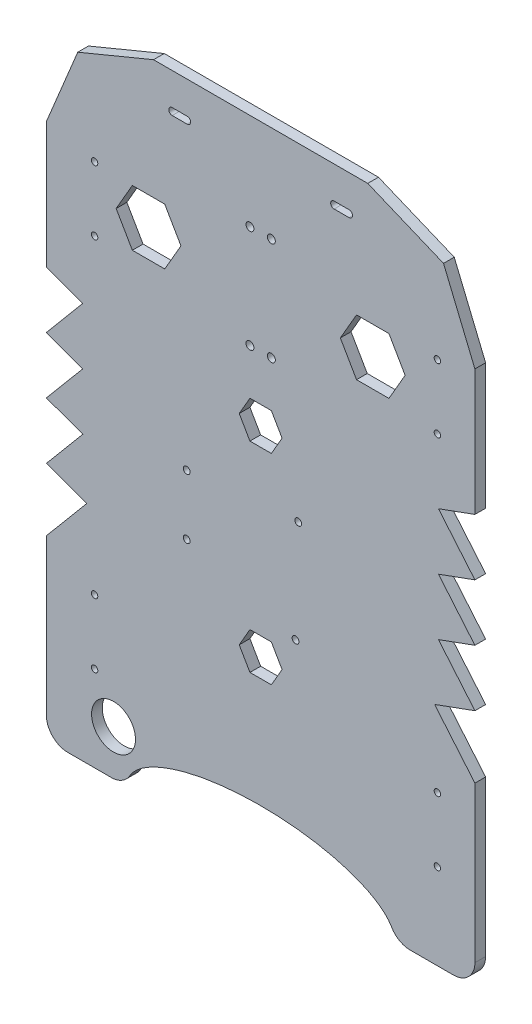
SolidWorks part; units mm, degrees
ref_plane "前视基准面" through (0, 0, 0) normal (0, 0, 1) x (1, 0, 0)
ref_plane "上视基准面" through (0, 0, 0) normal (0, 1, 0) x (1, 0, 0)
ref_plane "右视基准面" through (0, 0, 0) normal (1, 0, 0) x (0, 0, -1)
sketch "草图1" plane through (0, 0, 0) normal (0, 0, 1) x (1, 0, 0)
  line L0 (-34.522, -8.1881) -> (17.5507, -3.1071)
  line L1 (100, -150) -> (-100, -150)
  line L2 (100, -150) -> (100, 100)
  line L3 (50, 150) -> (-50, 150)
  line L4 (-100, -150) -> (-100, 100)
  line L5 (100, -150) -> (-100, 150) construction
  line L6 (100, 150) -> (-100, -150) construction
  line L7 (17.5507, -3.1071) -> (16.2847, -51.3573)
  line L8 (16.2847, -51.3573) -> (-34.522, -36.1281)
  line L9 (-34.522, -36.1281) -> (-34.522, -8.1881)
  arc A0 (100, 100) -> (50, 150) centre (50, 100) ccw
  arc A1 (-50, 150) -> (-100, 100) centre (-50, 100) ccw
  circle A2 centre (-34.522, -8.1881) radius 1.6
  circle A3 centre (17.5507, -3.1071) radius 1.6
  circle A4 centre (16.2847, -51.3573) radius 1.6
  circle A5 centre (-34.522, -36.1281) radius 1.6
  point P0 (0, 0)
  dimension "D3" = 50
  dimension "D9" = 3.2
  dimension "D10" = 3.2
  dimension "D11" = 3.2
  dimension "D12" = 3.2
  dimension "D1" = 200
  dimension "D2" = 300
  dimension "D4" = 27.94
  dimension "D5" = 66.67
  dimension "D6" = 52.32
  dimension "D7" = 61.66
  dimension "D8" = 53.04
extrude "凸台-拉伸1" add sketch "草图1" against normal blind 5 contours L3 A1 L4 L1 L2 A0 A5 L9 A2 L0 A3 L7 A4 L8 | A5 L8 A4 L7 A3 L0 A2 L9
sketch "草图2" plane through (0, 0, 0) normal (0, 0, 1) x (1, 0, 0)
  line L0 (50, 150) -> (-50, 150) construction
  line L1 (-77.5, 95) -> (82.5, 95)
  line L2 (-77.5, 95) -> (-77.5, 65)
  line L3 (-77.5, 65) -> (82.5, 65)
  line L4 (82.5, 95) -> (82.5, 65)
  line L5 (-77.5, -80) -> (82.5, -80)
  line L6 (-77.5, -80) -> (-77.5, -110)
  line L7 (-77.5, -110) -> (82.5, -110)
  line L8 (82.5, -80) -> (82.5, -110)
  line L9 (100, -150) -> (100, 100) construction
  line L10 (100, -150) -> (-100, -150) construction
  circle A0 centre (-77.5, 95) radius 1.5
  circle A1 centre (-77.5, 65) radius 1.5
  circle A2 centre (82.5, 95) radius 1.5
  circle A3 centre (82.5, 65) radius 1.5
  circle A4 centre (82.5, -80) radius 1.5
  circle A5 centre (82.5, -110) radius 1.5
  circle A6 centre (-77.5, -110) radius 1.5
  circle A7 centre (-77.5, -80) radius 1.5
  dimension "D9" = 3
  dimension "D1" = 55
  dimension "D2" = 17.5
  dimension "D3" = 160
  dimension "D4" = 30
  dimension "D5" = 40
  dimension "D6" = 30
  dimension "D7" = 17.5
  dimension "D8" = 160
extrude "切除-拉伸1" cut sketch "草图2" against normal blind 10 contours L1 A0 L2 | L2 A0 L1 | L2 A1 L3 | L3 A1 L2 | L4 A2 L1 | L1 A2 L4 | L3 A3 L4 | L4 A3 L3 | L5 A4 L8 | L7 A5 L8 | L8 A4 L5 | L8 A5 L7 | L7 A6 L6 | L6 A6 L7 | L6 A7 L5 | L5 A7 L6
sketch "草图3" plane through (0, 0, 0) normal (0, 0, 1) x (1, 0, 0)
  line L0 (0, 150) -> (0, -150) construction
  line L1 (50, 150) -> (-50, 150) construction
  line L2 (100, -150) -> (-100, -150) construction
  circle A0 centre (-5, 105) radius 1.85
  circle A1 centre (5, 105) radius 1.85
  circle A2 centre (-5, 57) radius 1.85
  circle A3 centre (5, 57) radius 1.85
  dimension "D2" = 3.7
  dimension "D4" = 3.7
  dimension "D1" = 10
  dimension "D3" = 45
  dimension "D5" = 48
  dimension "D6" = 10
extrude "切除-拉伸2" cut sketch "草图3" against normal blind 10
sketch "草图4" plane through (0, 0, 0) normal (0, 0, 1) x (1, 0, 0)
  circle A0 centre (-68.6677, -128.9563) radius 10.25
  dimension "D1" = 20.5
extrude "切除-拉伸3" cut sketch "草图4" against normal blind 10
sketch "草图5" plane through (0, 0, 0) normal (0, 0, 1) x (1, 0, 0)
  line L0 (100, -150) -> (-100, -150) construction
  ellipse E0 centre (0, -150) end of major axis (62.5366, -150) minor radius 23.4961
extrude "切除-拉伸4" cut sketch "草图5" against normal blind 10
fillet "圆角1" radius 10 4 edges at (100, -150, -2.5) (62.5366, -150, -2.5) (-62.5366, -150, -2.5) (-100, -150, -2.5)
sketch "草图6" plane through (0, 0, 0) normal (0, 0, 1) x (1, 0, 0)
  line L0 (44.7566, 68.037) -> (37.195, 81.1341)
  line L3 (50, 150) -> (-50, 150) construction
  line L4 (0, 150) -> (0, -126.5039) construction
  line L11 (-37.195, 81.1341) -> (-44.7566, 94.2313)
  line L12 (-44.7566, 94.2313) -> (-59.8799, 94.2313)
  line L13 (-59.8799, 94.2313) -> (-67.4415, 81.1341)
  line L14 (-67.4415, 81.1341) -> (-59.8799, 68.037)
  line L15 (-59.8799, 68.037) -> (-44.7566, 68.037)
  line L16 (-44.7566, 68.037) -> (-37.195, 81.1341)
  line L17 (59.8799, 68.037) -> (44.7566, 68.037)
  line L18 (67.4415, 81.1341) -> (59.8799, 68.037)
  line L19 (59.8799, 94.2313) -> (67.4415, 81.1341)
  line L20 (44.7566, 94.2313) -> (59.8799, 94.2313)
  line L21 (37.195, 81.1341) -> (44.7566, 94.2313)
  circle A2 centre (-52.3182, 81.1341) radius 13.0971 construction
  ellipse E0 centre (0, -150) end of major axis (62.5366, -150) minor radius 23.4961 (61.1091, -145.0084) -> (-61.1091, -145.0084) ccw construction
extrude "切除-拉伸5" cut sketch "草图6" against normal blind 10
sketch "草图9" plane through (0, 0, 0) normal (0, 0, 1) x (1, 0, 0)
  line L0 (-100, 41.1875) -> (-83, 35)
  line L1 (-100, -140) -> (-100, 100) construction
  line L2 (-83, 35) -> (-100, 14.7402)
  line L3 (-100, 14.7402) -> (-83, 8.5527)
  line L4 (-83, 8.5527) -> (-100, -11.7071)
  line L5 (-100, -11.7071) -> (-83, -17.8946)
  line L6 (-83, -17.8946) -> (-100, -38.1544)
  line L7 (-100, -38.1544) -> (-81.1919, -45)
  line L8 (-81.1919, -45) -> (-100, -67.4146)
  line L9 (0, 150) -> (0, -126.5039) construction
  line L10 (50, 150) -> (-50, 150) construction
  line L11 (81.1919, -45) -> (100, -67.4146)
  line L12 (100, -38.1544) -> (81.1919, -45)
  line L13 (83, -17.8946) -> (100, -38.1544)
  line L14 (100, -11.7071) -> (83, -17.8946)
  line L15 (83, 8.5527) -> (100, -11.7071)
  line L16 (100, 14.7402) -> (83, 8.5527)
  line L17 (83, 35) -> (100, 14.7402)
  line L18 (100, 41.1875) -> (83, 35)
  line L19 (-100, 41.1875) -> (-100, -67.4146)
  line L20 (100, 41.1875) -> (100, -67.4146)
  line L21 (-69.7645, -150) -> (-90, -150) construction
  ellipse E0 centre (0, -150) end of major axis (62.5366, -150) minor radius 23.4961 (61.1091, -145.0084) -> (-61.1091, -145.0084) ccw construction
  point P32 (0, 0)
  point P33 (0, 0)
  point P34 (-83.7909, -150)
  point P37 (0, 0)
  line M38 (100, -140) -> (100, 100)
  line M42 (-100, 100) -> (-100, -140)
  dimension "D1" = 70
  dimension "D2" = 70
  dimension "D3" = 40
  dimension "D4" = 17
  dimension "D5" = 17
  dimension "D6" = 17
  dimension "D7" = 105
  dimension "D8" = 115
extrude "切除-拉伸6" cut sketch "草图9" against normal blind 10 contours L2 L0 M42 | L4 L3 M42 | L6 L5 M42 | L8 L7 M42 | L12 L11 M38 | L14 L13 M38 | L16 L15 M38 | L18 L17 M38
sketch "草图10" plane through (0, 0, 0) normal (0, 0, 1) x (1, 0, 0)
  line L0 (0, 150) -> (0, -126.5039)
  line L1 (50, 150) -> (-50, 150) construction
  line L3 (10, 27) -> (5, 35.6603)
  line L4 (5, 35.6603) -> (-5, 35.6603)
  line L5 (-5, 35.6603) -> (-10, 27)
  line L6 (-10, 27) -> (-5, 18.3397)
  line L7 (-5, 18.3397) -> (5, 18.3397)
  line L8 (5, 18.3397) -> (10, 27)
  line L9 (10, -66.5039) -> (5, -57.8436)
  line L10 (5, -57.8436) -> (-5, -57.8436)
  line L11 (-5, -57.8436) -> (-10, -66.5039)
  line L12 (-10, -66.5039) -> (-5, -75.1641)
  line L13 (-5, -75.1641) -> (5, -75.1641)
  line L14 (5, -75.1641) -> (10, -66.5039)
  circle A0 centre (0, 27) radius 10
  circle A1 centre (0, -66.5039) radius 10
  circle A2 centre (0, 27) radius 8.6603 construction
  circle A3 centre (0, -66.5039) radius 8.6603 construction
  ellipse E0 centre (0, -150) end of major axis (62.5366, -150) minor radius 23.4961 (61.1091, -145.0084) -> (-61.1091, -145.0084) ccw construction
  dimension "D1" = 20
  dimension "D2" = 20
  dimension "D3" = 123
  dimension "D4" = 60
extrude "切除-拉伸7" cut sketch "草图10" against normal blind 10 contours L0 A0 | L0 A0 | L0 A1 | L0 A1
sketch "草图12" plane through (0, 0, -5) normal (0, 0, -1) x (-1, 0, 0)
  line L0 (-100, 100) -> (-85.3553, 135.3553)
  line L1 (50, 150) -> (85.3553, 135.3553)
  line L2 (85.3553, 135.3553) -> (100, 100)
  line L3 (-85.3553, 135.3553) -> (-50, 150)
  arc A0 (100, 100) -> (50, 150) centre (50, 100) ccw construction
  arc A1 (-50, 150) -> (-100, 100) centre (-50, 100) ccw construction
  circle A2 centre (-50, 100) radius 50
  circle A3 centre (50, 100) radius 50
extrude "切除-拉伸8" cut sketch "草图12" against normal blind 10 contours L0 A2 | L3 A2 | L1 A3 | L2 A3
sketch "草图13" plane through (0, 0, -5) normal (0, 0, -1) x (-1, 0, 0)
  line L0 (0, 150) -> (0, -126.5039)
  line L1 (-50, 150) -> (50, 150) construction
  line L2 (-41.29, 133.4) -> (-34.29, 133.4) construction
  line L3 (-41.29, 135) -> (-34.29, 135)
  line L4 (-41.29, 131.8) -> (-34.29, 131.8)
  line L5 (41.29, 133.4) -> (34.29, 133.4) construction
  line L6 (41.29, 135) -> (34.29, 135)
  line L7 (41.29, 131.8) -> (34.29, 131.8)
  arc A0 (-41.29, 135) -> (-41.29, 131.8) centre (-41.29, 133.4) ccw
  arc A1 (-34.29, 131.8) -> (-34.29, 135) centre (-34.29, 133.4) ccw
  arc A2 (41.29, 135) -> (41.29, 131.8) centre (41.29, 133.4) cw
  arc A3 (34.29, 131.8) -> (34.29, 135) centre (34.29, 133.4) cw
  ellipse E0 centre (0, -150) end of major axis (-62.5366, -150) minor radius 23.4961 (61.1091, -145.0084) -> (-61.1091, -145.0084) ccw construction
  point P14 (-37.79, 133.4)
  point P21 (37.79, 133.4)
  point P26 (0, 0)
  dimension "D1" = 1.6
  dimension "D2" = 7
  dimension "D3" = 75.58
  dimension "D4" = 15
extrude "切除-拉伸9" cut sketch "草图13" against normal blind 10 contours L4 A1 L3 A0 | A3 L7 A2 L6
